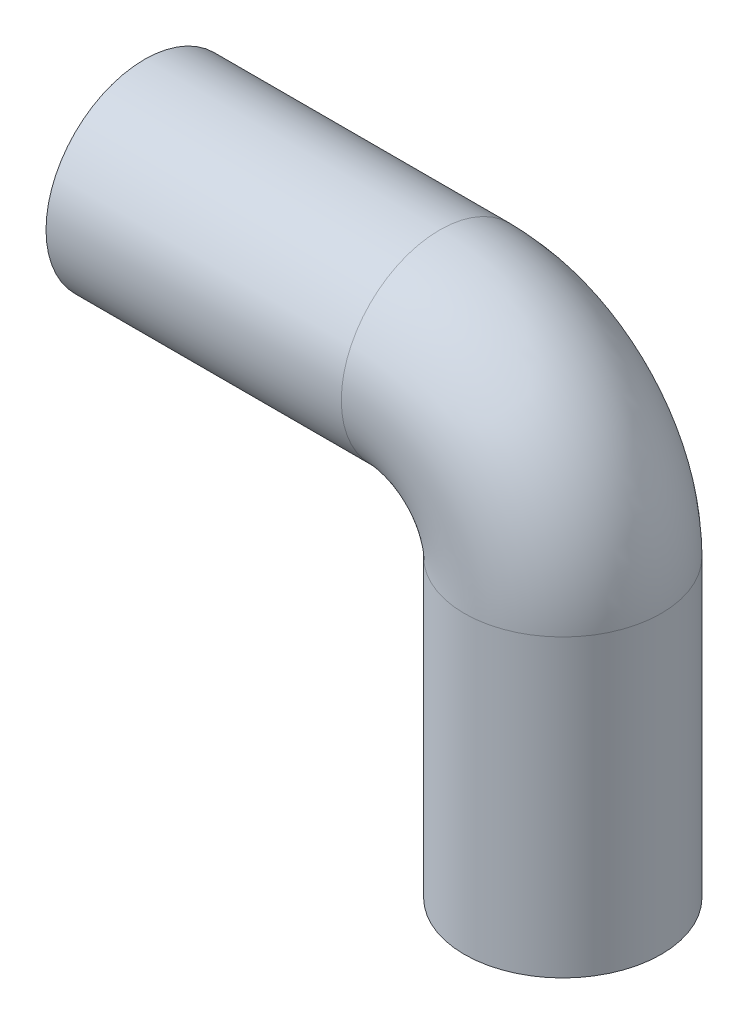
SolidWorks part; units mm, degrees
ref_plane "Front Plane" through (0, 0, 0) normal (0, 0, 1) x (1, 0, 0)
ref_plane "Top Plane" through (0, 0, 0) normal (0, 1, 0) x (1, 0, 0)
ref_plane "Right Plane" through (0, 0, 0) normal (1, 0, 0) x (0, 0, -1)
sketch "Sketch1" plane through (0, 0, 0) normal (0, 0, 1) x (1, 0, 0)
  line L0 (0, 0) -> (0, 152.4)
  line L1 (-63.5, 215.9) -> (-215.9, 215.9)
  arc A2 (0, 152.4) -> (-63.5, 215.9) centre (-63.5, 152.4) ccw
  point P7 (0, 215.9)
  point P8 (0, 0)
  dimension "D1" = 152.4
  dimension "D2" = 152.4
  dimension "D3" = 63.5
sketch "Sketch2" plane through (0, 0, 0) normal (0, 1, 0) x (1, 0, 0)
  circle A0 centre (0, 0) radius 50.8
  dimension "D1" = 101.6
sweep "Sweep1" add profiles "Sketch2" path "Sketch1"
shell "Shell2" thickness 2.54
